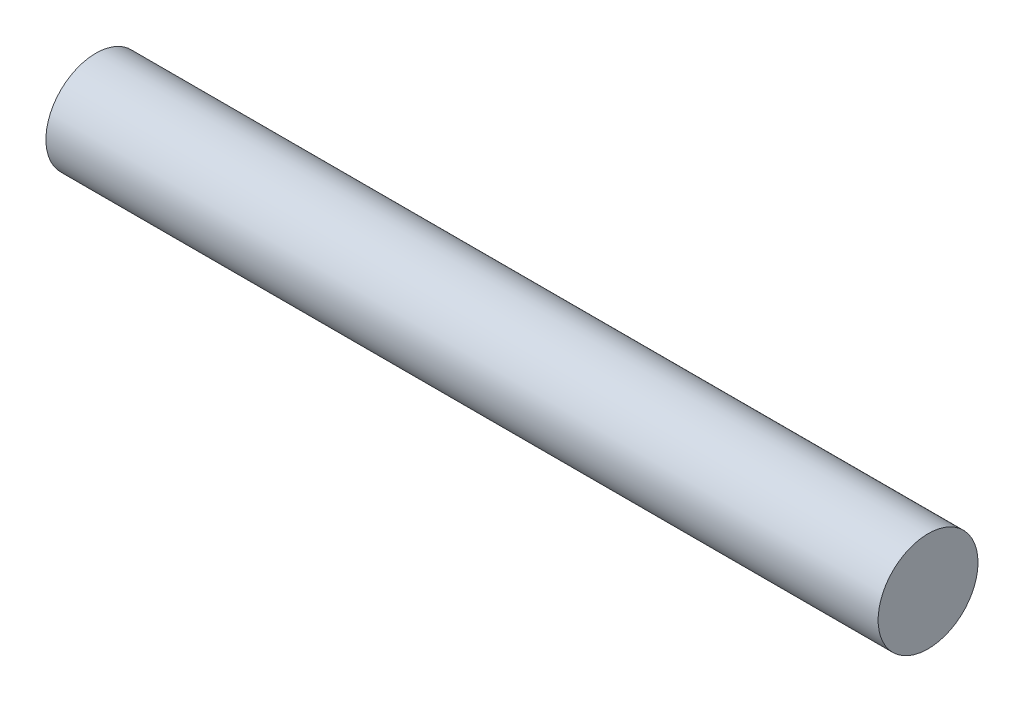
SolidWorks part; units mm, degrees
ref_plane "Piano frontale" through (0, 0, 0) normal (0, 0, 1) x (1, 0, 0)
ref_plane "Piano superiore" through (0, 0, 0) normal (0, 1, 0) x (1, 0, 0)
ref_plane "Piano destro" through (0, 0, 0) normal (1, 0, 0) x (0, 0, -1)
sketch "Schizzo1" plane through (0, 0, 0) normal (0, 0, 1) x (1, 0, 0)
  line L0 (28.0973, 0) -> (-26.3381, 0) construction
  line L1 (-25, 0) -> (-25, 1.5)
  line L2 (-25, 1.5) -> (0, 1.5)
  line L7 (0, 1.5) -> (0, 0)
  line L8 (-25, 0) -> (0, 0)
  point P7 (0, 0.75)
  dimension "D1" = 25
  dimension "D2" = 1.5
revolve "Rivoluzione1" add sketch "Schizzo1" angle 360 about L0
